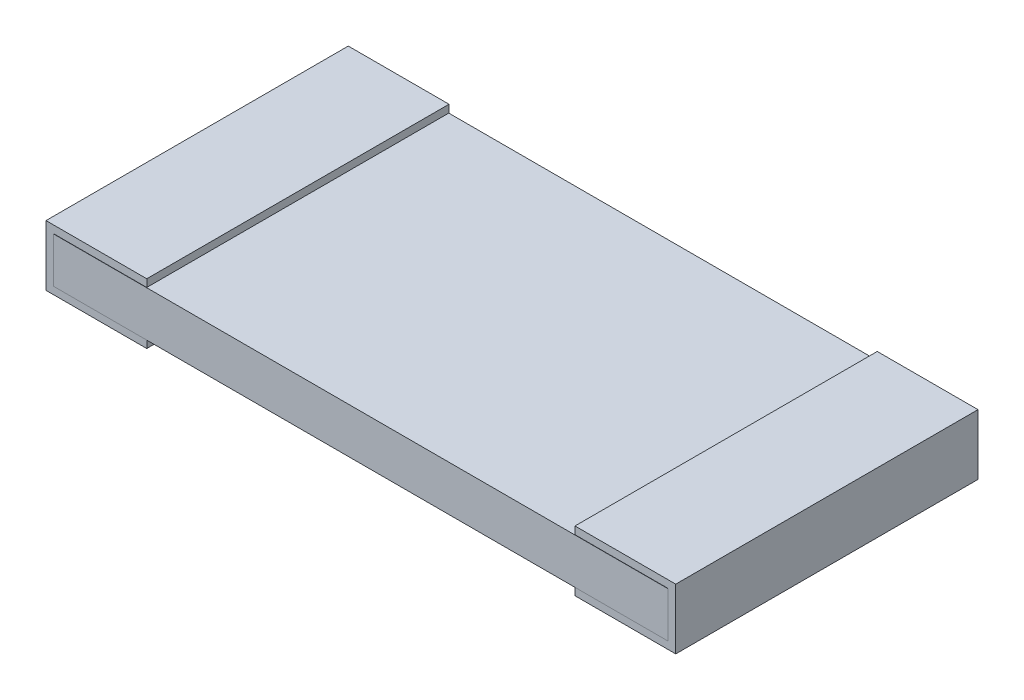
SolidWorks part; units mm, degrees
ref_plane "Front Plane" through (0, 0, 0) normal (0, 0, 1) x (1, 0, 0)
ref_plane "Top Plane" through (0, 0, 0) normal (0, 1, 0) x (1, 0, 0)
ref_plane "Right Plane" through (0, 0, 0) normal (1, 0, 0) x (0, 0, -1)
sketch "Sketch1" plane through (0, 0, 0) normal (0, 0, 1) x (1, 0, 0)
  line L0 (6.2738, 0.0762) -> (0.0762, 0.0762)
  line L1 (6.2738, 0.0762) -> (6.2738, 0.5334)
  line L2 (0.0762, 0.5334) -> (6.2738, 0.5334)
  line L3 (0.0762, 0.5334) -> (0.0762, 0.0762)
  dimension "D1" = 6.1976
  dimension "D2" = 0.4572
  dimension "D3" = 0.0762
  dimension "D4" = 0.0762
extrude "Base-Extrude" add sketch "Sketch1" against normal mid plane 3.048
ref_plane "Plane1" through (0, 0, -1.5265) normal (0, 0, -1) x (-1, 0, 0)
sketch "Sketch2" plane through (0, 0, -1.5265) normal (0, 0, -1) x (-1, 0, 0)
  line L0 (0, 0) -> (-1.016, 0)
  line L1 (0, 0) -> (0, 0.6096)
  line L2 (0, 0.6096) -> (-1.016, 0.6096)
  line L3 (-1.016, 0.6096) -> (-1.016, 0.5334)
  line L4 (-6.2738, 0.5334) -> (-0.0762, 0.5334) construction
  line L5 (-1.016, 0) -> (-1.016, 0.0762)
  line L6 (-0.0762, 0.0762) -> (-6.2738, 0.0762) construction
  line L7 (-0.0762, 0.5334) -> (-0.0762, 0.0762) construction
  line L8 (-0.0762, 0.0762) -> (-1.016, 0.0762)
  line L9 (-1.016, 0.5334) -> (-0.0762, 0.5334)
  line L10 (-0.0762, 0.5334) -> (-0.0762, 0.0762)
  dimension "D1" = 1.016
  dimension "D2" = 1.016
  dimension "D3" = 0.0762
extrude "Boss-Extrude1" add sketch "Sketch2" against normal blind 3.048
ref_plane "Plane2" through (3.175, 0, 0) normal (1, 0, 0) x (0, 0, -1)
mirror "Mirror1" about plane through (3.175, 0, 0) normal (1, 0, 0) of "Boss-Extrude1"
sketch "Component_Outline" plane through (0, 0, 0) normal (0, 1, 0) x (1, 0, 0)
  line L1 (0, -1.5215) -> (6.35, -1.5215)
  line L2 (0, -1.5215) -> (0, 1.5265)
  line L3 (0, 1.5265) -> (6.35, 1.5265)
  line L4 (6.35, -1.5215) -> (6.35, 1.5265)
